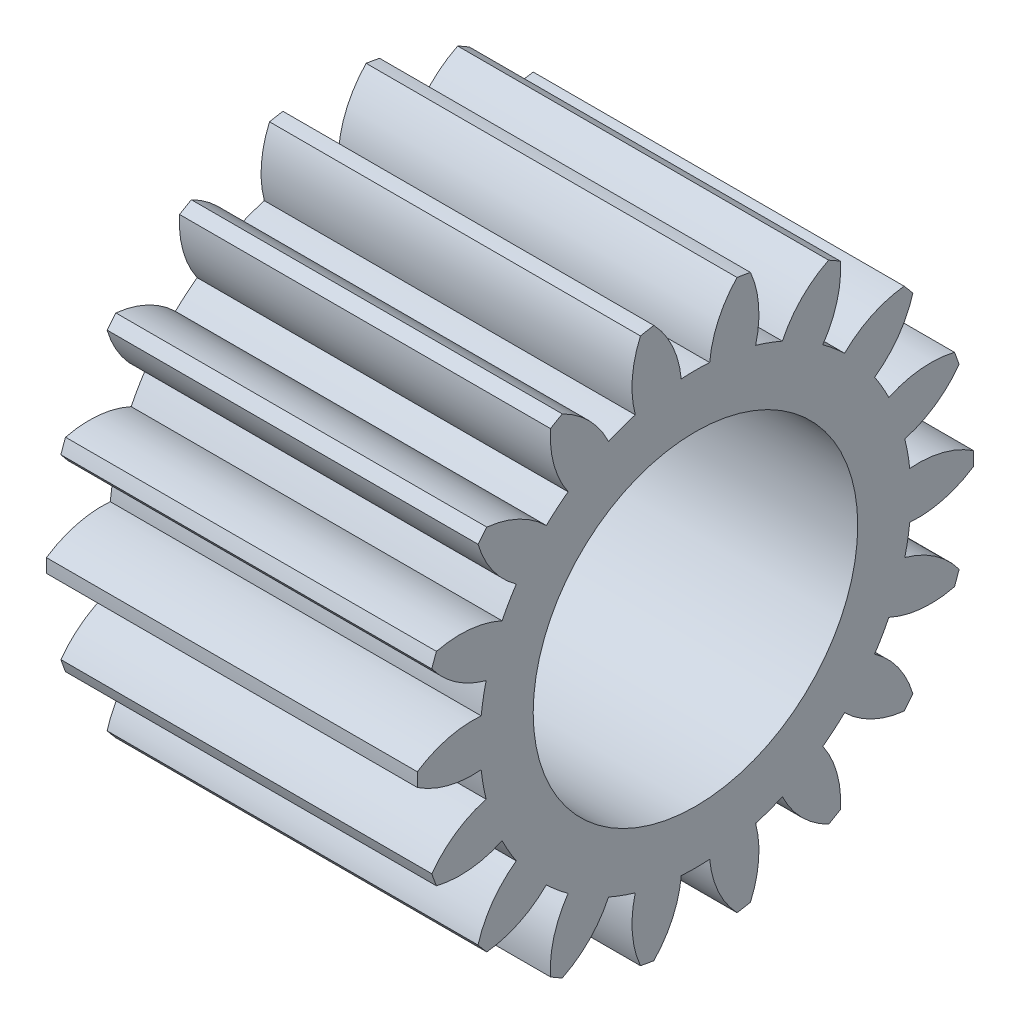
SolidWorks part; units mm, degrees
ref_plane "Plane1" through (0, 0, 0) normal (0, 0, 1) x (1, 0, 0)
ref_plane "Plane2" through (0, 0, 0) normal (0, 1, 0) x (1, 0, 0)
ref_plane "Plane3" through (0, 0, 0) normal (1, 0, 0) x (0, 0, -1)
other "Configuration Table"
sketch "HoldingSke" plane through (0, 0, 0) normal (0, 1, 0) x (1, 0, 0)
  line L0 (0, 0) -> (1.5851, -0.515)
  line L1 (-15, 0) -> (100, 0) construction
  line L2 (0, 0) -> (-2.1039, 2.3779)
  line L3 (0, 0) -> (-11.863, 4.5341)
  line L4 (0, 0) -> (8.2133, 2.6687)
  line L5 (0, 0) -> (-46.8476, -17.4728)
  line L6 (0, 0) -> (-6.6317, -4.4744)
  line L7 (-2.1039, 2.3779) -> (8.6586, 51.2059)
  line L8 (-76.2, 54.61) -> (-76.1, 54.61)
  line L9 (-71.009, 38.7566) -> (-53.1078, 45.2721)
  line L10 (-76.2, 71.12) -> (104.1128, 71.12)
  line L11 (0, 0) -> (-8, 0)
  line L12 (-76.2, 101.6) -> (-76.177, 101.6)
  line L13 (24.9733, 27.94) -> (52.9518, 28.4284)
  line L14 (24.9733, 27.94) -> (24.9743, 27.94)
  line L15 (24.9733, 27.94) -> (100.4006, 29.5858)
  line L16 (-63.627, -0.6) -> (-12.827, -0.6)
  circle A0 centre (0, 0) radius 0.5
  circle A1 centre (0, 0) radius 4.649
  circle A2 centre (0, 0) radius 37.5
  circle A3 centre (0, 0) radius 0.5
  dimension "MHD" = 9.298
  dimension "Hub_dia" = 75
  dimension "Bore" = 1
  dimension "MBD" = 1
  dimension "Num_teeth" = 18
  dimension "Pitch" = 1.6667
  dimension "Overall_len" = 50
  dimension "Show_teeth" = 18
  dimension "Thickness" = 8
  dimension "OAL" = 50.0001
  dimension "T_dim" = 0.1
  dimension "Ap" = 20
  dimension "H" = 19.05
  dimension "Pitch_radius" = 180.3128
  dimension "Width" = 8
  dimension "Backlash" = 0.023
  dimension "Addendum_fac" = 1
  dimension "Dedendum_fac" = 1.25
  dimension "Clearance_fac" = 0.25
  dimension "Dedendum_add" = 0.001
  dimension "Module" = 0.6
sketch "BasProSke" plane through (0, 0, 0) normal (0, 1, 0) x (1, 0, 0)
  line L0 (-10, 0) -> (60, 0) construction
  line L1 (0, 0) -> (0, 6)
  line L2 (0, 0) -> (8, 0)
  line L3 (8, 0) -> (8, 6)
  line L4 (8, 6) -> (0, 6)
  dimension "Thickness" = 8
  dimension "Diameter" = 12
revolve "Base-Revolve" add sketch "BasProSke" angle 360 about L0
sketch "TooCutSke" plane through (0, 0, 0) normal (1, 0, 0) x (0, 0, -1)
  line L1 (0, 0) -> (0, 107) construction
  line L2 (0, 0) -> (-0.5109, 5.3758) construction
  line L3 (0, 0) -> (-1.8694, 10.6021) construction
  line L4 (-0.5109, 5.3758) -> (-0.9347, 5.301) construction
  arc A0 (0.3066, 4.6389) -> (-0.3066, 4.6389) centre (0, 0) ccw
  arc A1 (0.9183, 5.955) -> (-0.9183, 5.955) centre (0, 0) ccw
  circle A2 centre (0, 0) radius 5.4 construction
  circle A3 centre (0, 0) radius 5.0743 construction
  arc A4 (-0.3066, 4.6389) -> (-0.9183, 5.955) centre (-2.4574, 4.4396) ccw
  arc A5 (0.9183, 5.955) -> (0.3066, 4.6389) centre (2.4574, 4.4396) ccw
  dimension "Root_dia" = 9.298
  dimension "Overcut_dia" = 12.0508
  dimension "Pitch_dia" = 10.8
  dimension "Base_dia" = 10.1487
  dimension "Flank_rad" = 2.16
  dimension "Half_ang" = 10
  dimension "Half_CT" = 0.4304
extrude "ToothCut" cut sketch "TooCutSke" along normal through all
fillet "Breaks" [suppressed] radius 0.012
fillet "RootFillets" [suppressed] radius 0.151
pattern_circular "TeethCuts" count 18 every 20 about axis through (-10, 0, 0) along (1, 0, 0) of "ToothCut", "RootFillets", "Breaks"
sketch "HubNeaOneSke" plane through (0, 0, 0) normal (-1, 0, 0) x (0, 0, 1)
  circle A0 centre (0, 0) radius 4.649
  dimension "Diameter" = 9.298
extrude "HubNearOne" [suppressed] add sketch "HubNeaOneSke" along normal blind 42.0001
sketch "HubNeaBotSke" plane through (0, 0, 0) normal (-1, 0, 0) x (0, 0, 1)
  circle A0 centre (0, 0) radius 4.649
  dimension "Diameter" = 9.298
extrude "HubNearBoth" [suppressed] add sketch "HubNeaBotSke" along normal blind 21
ref_plane "FarPln" through (8, 0, 0) normal (1, 0, 0) x (0, 0, -1)
sketch "HubFarSke" plane through (8, 0, 0) normal (1, 0, 0) x (0, 0, -1)
  circle A0 centre (0, 0) radius 4.649
  dimension "Diameter" = 9.298
extrude "HubFar" [suppressed] add sketch "HubFarSke" along normal blind 21
sketch "BorSke" plane through (0, 0, 0) normal (1, 0, 0) x (0, 0, -1)
  circle A0 centre (0, 0) radius 0.5
  dimension "Diameter" = 1
extrude "Bore" cut sketch "BorSke" along normal mid plane 100.0001
sketch "KeySke" plane through (0, 0, 0) normal (1, 0, 0) x (0, 0, -1)
  line L0 (-0.05, 0) -> (-0.05, 0.6)
  line L1 (-0.05, 0.6) -> (0.05, 0.6)
  line L2 (0.05, 0.6) -> (0.05, 0)
  line L3 (0, 0) -> (0, 34) construction
  line L4 (-0.05, 0) -> (0.05, 0)
  dimension "Offset" = 0.6
  dimension "Width" = 0.1
extrude "Keyway" [suppressed] cut sketch "KeySke" along normal mid plane 100.0001
pattern_circular "Keyway2" [suppressed] count 2 every 90 about axis through (-10, 0, 0) along (1, 0, 0)
sketch "Sketch1" plane through (8, 0, 0) normal (1, 0, 0) x (0, 0, -1)
  circle A0 centre (0, 0) radius 3.5
  dimension "D1" = 7
extrude "Cut-Extrude1" cut sketch "Sketch1" against normal through all
equation "' \"Module@HoldingSke\" = 6.35"
equation "' \"Num_teeth@HoldingSke\" = 12"
equation "' \"Ap@HoldingSke\" =  20"
equation "' \"Ap@HoldingSke\" = 20"
equation "' \"Width@HoldingSke\" = 0.5 * 25.4"
equation "' \"Hub_dia@HoldingSke\"= 1 * 25.4"
equation "' \"Hub_dia@HoldingSke\" = 1 * 25.4"
equation "' \"Overall_len@HoldingSke\" = 1.0 * 25.4"
equation "' \"Bore@HoldingSke\" = 0.75 * 25.4"
equation "' \"T_dim@HoldingSke\" = 0.1 * 25.4"
equation "' \"Width@KeySke\" = 0.25 * 25.4"
equation "' \"Show_teeth@HoldingSke\" = 13"
equation "' \"Backlash@HoldingSke\" = 0.009 * 25.4"
equation "' \"Addendum_fac@HoldingSke\" = 1.0"
equation "' \"Dedendum_fac@HoldingSke\" = 1.25"
equation "' \"Dedendum_add@HoldingSke\" = 0.00005 * 25.4"
equation "' \"Clearance_fac@HoldingSke\" = 0.25"
equation "\"Pitch@HoldingSke\" = 1 / \"Module@HoldingSke\""
equation "\"Overcut_dia@TooCutSke\" = (\"Num_teeth@HoldingSke\" + 2 * \"Addendum_fac@HoldingSke\") / \"Pitch@HoldingSke\" + 0.002 * 25.4"
equation "\"Pitch_dia@TooCutSke\" = \"Num_teeth@HoldingSke\" / \"Pitch@HoldingSke\""
equation "\"Base_dia@TooCutSke\" = \"Num_teeth@HoldingSke\" / \"Pitch@HoldingSke\" * cos((\"Ap@HoldingSke\"  * 3.14159265 / 180))"
equation "\"Root_dia@TooCutSke\" = (\"Num_teeth@HoldingSke\" + 2) / \"Pitch@HoldingSke\" - 2 * (\"Addendum_fac@HoldingSke\" + \"Dedendum_fac@HoldingSke\") / \"Pitch@HoldingSke\" - \"Dedendum_add@HoldingSke\" * 2"
equation "\"Half_ang@TooCutSke\" = 180 / \"Num_teeth@HoldingSke\""
equation "\"Half_CT@TooCutSke\" = \"Num_teeth@HoldingSke\" / \"Pitch@HoldingSke\" * sin((3.14159265 / 2 / \"Num_teeth@HoldingSke\")) / 2 - 7 * \"Backlash@HoldingSke\" / 4"
equation "\"Flank_rad@TooCutSke\" = \"Num_teeth@HoldingSke\" / \"Pitch@HoldingSke\" / 5"
equation "\"Radius@RootFillets\" = \"Clearance_fac@HoldingSke\" / \"Pitch@HoldingSke\" + \"Dedendum_add@HoldingSke\""
equation "\"Break_rad@Breaks\" = 0.02 / \"Pitch@HoldingSke\""
equation "\"Thickness@HoldingSke\" = \"Width@HoldingSke\""
equation "\"OAL@HoldingSke\" = \"Thickness@HoldingSke\""
equation "\"MHD@HoldingSke\" = (\"Num_teeth@HoldingSke\" + 2) / \"Pitch@HoldingSke\" - 2 * (\"Addendum_fac@HoldingSke\" + \"Dedendum_fac@HoldingSke\")  / \"Pitch@HoldingSke\" - \"Dedendum_add@HoldingSke\" * 2"
equation "\"MBD@HoldingSke\" = (\"Num_teeth@HoldingSke\" + 2) / \"Pitch@HoldingSke\" - 2 * (\"Addendum_fac@HoldingSke\" + \"Dedendum_fac@HoldingSke\")  / \"Pitch@HoldingSke\" - \"Dedendum_add@HoldingSke\" * 2 - 0.002 * 25.4"
equation "\"MHD@HoldingSke\" = ((sgn( \"MHD@HoldingSke\" - \"Hub_dia@HoldingSke\" )-1)*( \"MHD@HoldingSke\" - \"Hub_dia@HoldingSke\" ))/-2+ \"Hub_dia@HoldingSke\""
equation "\"MBD@HoldingSke\" = ((sgn( \"MBD@HoldingSke\" - \"Bore@HoldingSke\" )-1)*( \"MBD@HoldingSke\" - \"Bore@HoldingSke\" ))/-2+ \"Bore@HoldingSke\""
equation "\"OAL@HoldingSke\" = ((sgn( \"OAL@HoldingSke\" - \"Overall_len@HoldingSke\" )+1)*( \"OAL@HoldingSke\" - \"Overall_len@HoldingSke\" ))/2 + \"Overall_len@HoldingSke\" + 0.000002 * 25.4"
equation "\"Num_teeth@TeethCuts\" = int( \"Show_teeth@HoldingSke\" ) + 1"
equation "\"Num_teeth@TeethCuts\" = ((sgn( \"Num_teeth@TeethCuts\" - \"Num_teeth@HoldingSke\" )-1)*( \"Num_teeth@TeethCuts\" - \"Num_teeth@HoldingSke\" ))/-2+ \"Num_teeth@HoldingSke\""
equation "\"Num_teeth@TeethCuts\" = ((sgn( \"Num_teeth@TeethCuts\" - 2.0)+1)*( \"Num_teeth@TeethCuts\" - 2.0))/2 +2.0"
equation "\"Angle@TeethCuts\" = 360.0 / \"Num_teeth@HoldingSke\""
equation "\"Diameter@BasProSke\" = (\"Num_teeth@HoldingSke\" + 2 * \"Addendum_fac@HoldingSke\") / \"Pitch@HoldingSke\""
equation "\"Thickness@BasProSke\"  = \"Thickness@HoldingSke\""
equation "' \"Fillet_rad@BasProSke\" =  \"Thickness@HoldingSke\" * 0.05"
equation "' \"Fillet_rad@BasProSke\" = \"Thickness@HoldingSke\" * 0.05"
equation "\"MHD@HoldingSke\" = ((sgn( \"MHD@HoldingSke\" - \"Root_dia@TooCutSke\" )-1)*( \"MHD@HoldingSke\" - \"Root_dia@TooCutSke\" ))/-2+ \"Root_dia@TooCutSke\""
equation "\"Diameter@HubNeaOneSke\" = \"MHD@HoldingSke\""
equation "\"Length@HubNearOne\" = \"OAL@HoldingSke\" - \"Thickness@BasProSke\""
equation "\"Diameter@HubNeaBotSke\" = \"MHD@HoldingSke\""
equation "\"Length@HubNearBoth\" = ( \"OAL@HoldingSke\" - \"Thickness@BasProSke\" ) / 2.0"
equation "\"Thickness@FarPln\" = \"Thickness@BasProSke\""
equation "\"Diameter@HubFarSke\" = \"MHD@HoldingSke\""
equation "\"Length@HubFar\" = ( \"OAL@HoldingSke\" - \"Thickness@BasProSke\" ) / 2.0"
equation "\"Diameter@BorSke\" = \"MBD@HoldingSke\""
equation "\"D1@Bore\" = \"OAL@HoldingSke\" * 2.0"
equation "\"D1@Keyway\" = \"OAL@HoldingSke\" * 2.0"
equation "\"Offset@KeySke\" = \"T_dim@HoldingSke\" + \"MBD@HoldingSke\" / 2.0"
